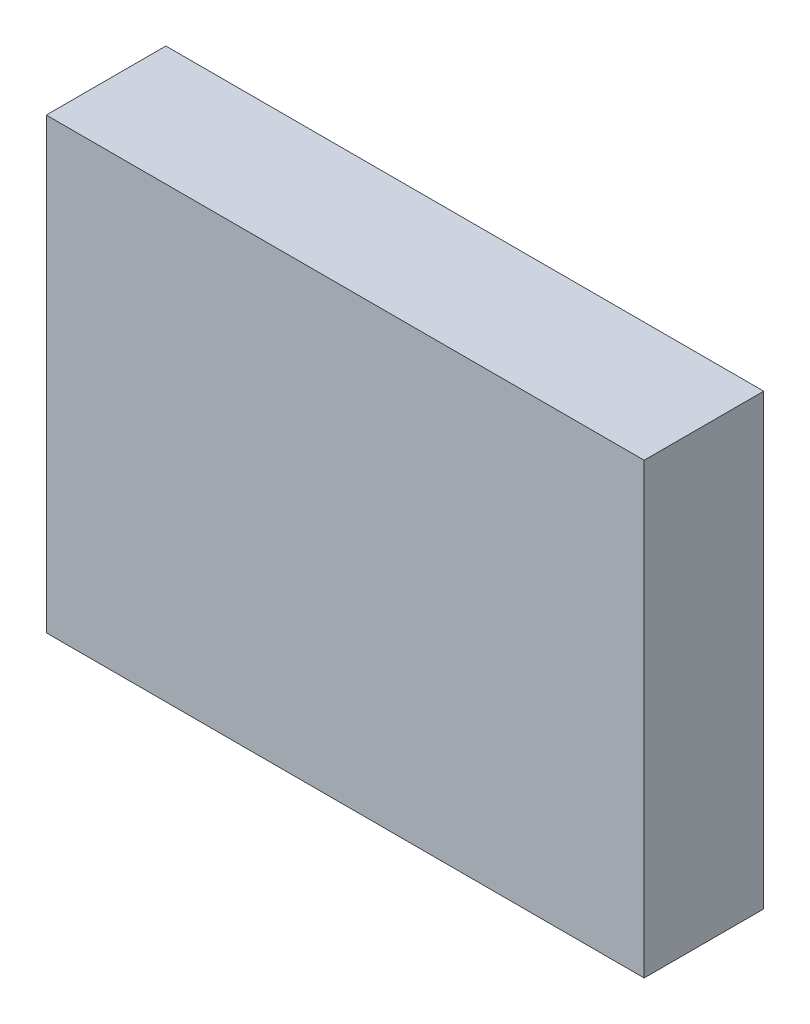
SolidWorks part; units mm, degrees
material "ALUMINUM 6061-T6"
ref_plane "Front Plane" through (0, 0, 0) normal (0, 0, 1) x (1, 0, 0)
ref_plane "Top Plane" through (0, 0, 0) normal (0, 1, 0) x (1, 0, 0)
ref_plane "Right Plane" through (0, 0, 0) normal (1, 0, 0) x (0, 0, -1)
sketch "Sketch1" plane through (0, 0, 0) normal (0, 0, 1) x (1, 0, 0)
  line L1 (-50, -37.5) -> (50, -37.5)
  line L2 (-50, -37.5) -> (-50, 37.5)
  line L3 (-50, 37.5) -> (50, 37.5)
  line L4 (50, -37.5) -> (50, 37.5)
  line L5 (-50, -37.5) -> (50, 37.5) construction
  line L6 (-50, 37.5) -> (50, -37.5) construction
  point P0 (0, 0)
  dimension "D1" = 100
  dimension "D2" = 75
extrude "Boss-Extrude1" add sketch "Sketch1" along normal mid plane 20
